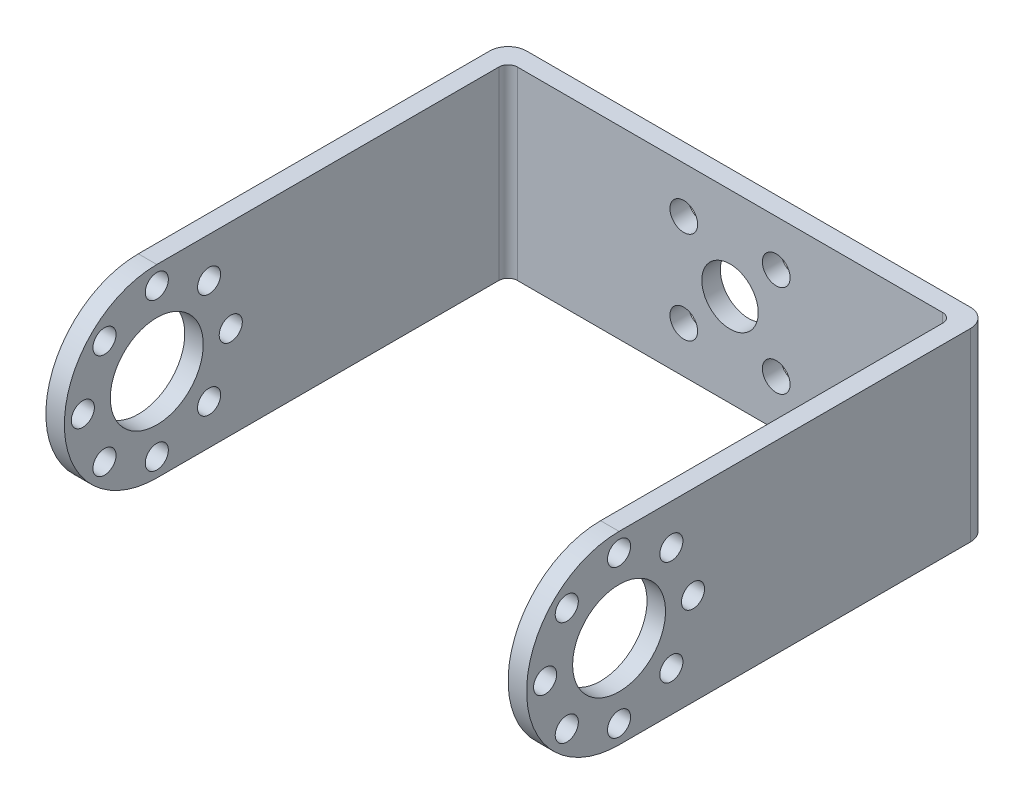
SolidWorks part; units mm, degrees
ref_plane "前视基准面" through (0, 0, 0) normal (0, 0, 1) x (1, 0, 0)
ref_plane "上视基准面" through (0, 0, 0) normal (0, 1, 0) x (1, 0, 0)
ref_plane "右视基准面" through (0, 0, 0) normal (1, 0, 0) x (0, 0, -1)
sketch "草图1" plane through (0, 0, 0) normal (0, 1, 0) x (1, 0, 0)
  line L0 (-19.3088, 32.0957) -> (32.6912, 32.0957)
  line L1 (32.6912, 32.0957) -> (32.6912, -17.9043)
  line L2 (32.6912, -17.9043) -> (30.6912, -17.9043)
  line L3 (30.6912, -17.9043) -> (30.6912, 30.0957)
  line L4 (30.6912, 30.0957) -> (-17.3088, 30.0957)
  line L5 (-17.3088, 30.0957) -> (-17.3088, -17.9043)
  line L6 (-17.3088, -17.9043) -> (-19.3088, -17.9043)
  line L7 (-19.3088, -17.9043) -> (-19.3088, 32.0957)
  dimension "D1" = 2
  dimension "D2" = 2
  dimension "D3" = 2
  dimension "D4" = 50
  dimension "D5" = 52
  dimension "D6" = 50
extrude "凸台-拉伸1" add sketch "草图1" along normal blind 20
fillet "圆角1" radius 2 2 edges at (32.6912, 10, -32.0957) (-19.3088, 10, -32.0957)
fillet "圆角2" radius 1 2 edges at (30.6912, 10, -30.0957) (-17.3088, 10, -30.0957)
sketch "草图2" plane through (-19.3088, 0, 0) normal (-1, 0, 0) x (0, 0, 1)
  line L0 (-30.0957, 0) -> (17.9043, 0) construction
  line L1 (17.9043, 20) -> (17.9043, 0) construction
  line L2 (7.9043, 20) -> (17.9043, 20)
  line L3 (17.9043, 20) -> (17.9043, 10)
  arc A0 (17.9043, 10) -> (7.9043, 20) centre (7.9043, 10) ccw
  dimension "D1" = 10
  dimension "D2" = 10
extrude "切除-拉伸1" cut sketch "草图2" against normal up to surface (52 mm away) up to face at (32.6912, 10, -6.0957)
sketch "草图3" plane through (-19.3088, 0, 0) normal (-1, 0, 0) x (0, 0, 1)
  line L0 (-30.0957, 0) -> (17.9043, 0) construction
  line L1 (17.9043, 10) -> (17.9043, 0) construction
  line L3 (7.9043, 0) -> (17.9043, 0)
  line L4 (17.9043, 0) -> (17.9043, 10)
  arc A0 (7.9043, 0) -> (17.9043, 10) centre (7.9043, 10) ccw
  dimension "D1" = 10
  dimension "D2" = 10
extrude "切除-拉伸2" cut sketch "草图3" against normal up to surface (52 mm away) up to face at (32.6912, 10.4142, -2.8814)
sketch "草图4" plane through (-19.3088, 0, 0) normal (-1, 0, 0) x (0, 0, 1)
  line L0 (-30.0957, 0) -> (7.9043, 0) construction
  circle A0 centre (7.9043, 10) radius 5.025
  arc A1 (7.9043, 0) -> (7.9043, 20) centre (7.9043, 10) ccw construction
  circle A2 centre (7.9043, 18) radius 1.25
  circle A3 centre (13.5612, 15.6569) radius 1.25
  circle A4 centre (15.9043, 10) radius 1.25
  circle A5 centre (13.5612, 4.3431) radius 1.25
  circle A6 centre (7.9043, 2) radius 1.25
  circle A7 centre (2.2475, 4.3431) radius 1.25
  circle A8 centre (-0.0957, 10) radius 1.25
  circle A9 centre (2.2475, 15.6569) radius 1.25
  point P7 (17.9043, 10)
  point P27 (7.9043, 10)
  dimension "D3" = 10.05
  dimension "D4" = 2.5
  dimension "D1" = 10
  dimension "D2" = 10
  dimension "D5" = 8
  dimension "D6" = 8
extrude "切除-拉伸3" cut sketch "草图4" against normal up to surface (52 mm away) up to face at (32.6912, 10, -8.5957)
sketch "草图5" plane through (0, 0, -32.0957) normal (0, 0, -1) x (-1, 0, 0)
  line L0 (-30.6912, 20) -> (17.3088, 20) construction
  line L1 (-32.6912, 0) -> (-32.6912, 20) construction
  circle A0 centre (-6.6912, 10) radius 3.05
  circle A1 centre (-11.6912, 15) radius 1.5
  circle A2 centre (-1.6912, 15) radius 1.5
  circle A5 centre (-1.6912, 5) radius 1.5
  circle A8 centre (-11.6912, 5) radius 1.5
  dimension "D4" = 3
  dimension "D8" = 6.1
  dimension "D1" = 10
  dimension "D2" = 26
  dimension "D3" = 5
  dimension "D5" = 5
  dimension "D6" = 2
  dimension "D7" = 2
extrude "切除-拉伸4" cut sketch "草图5" against normal up to next
